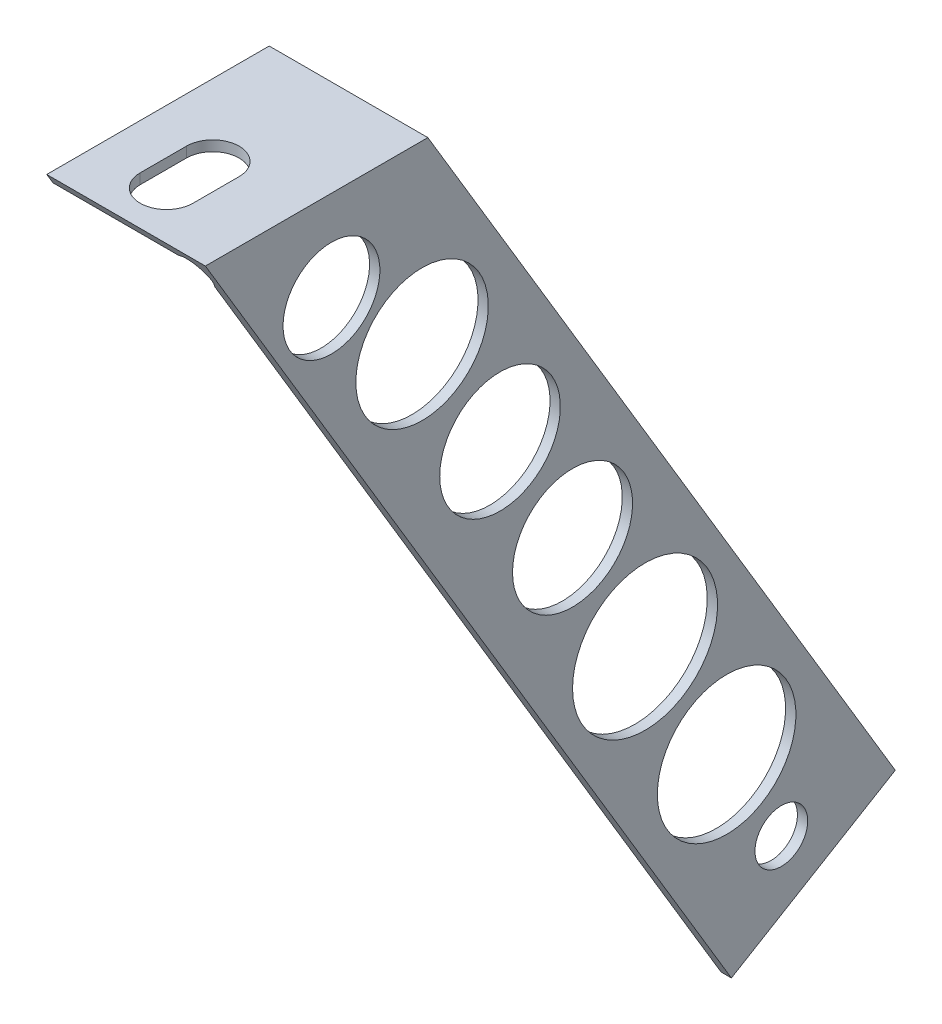
SolidWorks part; units mm, degrees
ref_plane "Front Plane" through (0, 0, 0) normal (0, 0, 1) x (1, 0, 0)
ref_plane "Top Plane" through (0, 0, 0) normal (0, 1, 0) x (1, 0, 0)
ref_plane "Right Plane" through (0, 0, 0) normal (1, 0, 0) x (0, 0, -1)
sketch "Sketch1" plane through (0, 0, 0) normal (1, 0, 0) x (0, 0, -1)
  line L0 (-193.675, 0) -> (193.675, 0)
  line L1 (193.675, 0) -> (239.395, -132.715)
  line L2 (239.395, -132.715) -> (239.395, -161.29)
  line L3 (239.395, -161.29) -> (-243.205, -161.29)
  line L4 (-243.205, -161.29) -> (-243.205, -132.715)
  line L5 (-243.205, -132.715) -> (-193.675, 0)
  line L6 (219.075, -116.84) -> (219.075, 0) construction
  line L7 (219.075, -116.84) -> (233.9261, -116.84) construction
  line L8 (142.875, 0) -> (142.875, -116.84) construction
  line L9 (219.075, -116.84) -> (219.075, -161.29) construction
  circle A0 centre (219.075, -116.84) radius 4.064
  circle A1 centre (219.075, -116.84) radius 8.6233 construction
  circle A2 centre (142.875, 0) radius 4.064 construction
  circle A3 centre (-31.115, 0) radius 4.064 construction
  point P9 (0, 0)
  dimension "D8" = 8.128
  dimension "D11" = 17.2466
  dimension "D3" = 8.128
  dimension "D9" = 8.128
  dimension "D1" = 387.35
  dimension "D2" = 173.99
  dimension "D4" = 482.6
  dimension "D5" = 110.466
  dimension "D6" = 20.32
  dimension "D7" = 161.29
  dimension "D10" = 116.84
  dimension "D12" = 76.2
  dimension "D13" = 50.8
extrude "Boss-Extrude1" add sketch "Sketch1" along normal blind 2.032
sketch "Sketch2" plane through (0, 0, 0) normal (0, 1, 0) x (1, 0, 0)
  line L2 (-13.843, 144.8435) -> (-13.843, 137.7315)
  line L4 (-5.715, 144.8435) -> (-5.715, 137.7315)
  line L5 (2.032, -193.675) -> (2.032, 193.675)
  line L6 (2.032, 193.675) -> (0, 193.675)
  line L7 (0, 193.675) -> (-20.828, 165.1)
  line L8 (-20.828, 165.1) -> (-20.828, -165.1)
  line L9 (-20.828, -165.1) -> (0, -193.675)
  line L10 (0, -193.675) -> (2.032, -193.675)
  line L11 (-13.843, 144.8435) -> (-5.715, 137.7315) construction
  line L12 (-13.843, 137.7315) -> (-5.715, 144.8435) construction
  circle A0 centre (-9.779, 141.2875) radius 4.064 construction
  circle A1 centre (-9.779, -32.7025) radius 4.064
  arc A2 (-13.843, 144.8435) -> (-5.715, 144.8435) centre (-9.779, 144.8435) cw
  arc A3 (-13.843, 137.7315) -> (-5.715, 137.7315) centre (-9.779, 137.7315) ccw
  point P0 (-20.828, 0)
  point P1 (2.032, 0)
  point P22 (-9.779, 148.9075)
  point P23 (-9.779, 133.6675)
  dimension "D3" = 8.128
  dimension "D4" = 8.128
  dimension "D5" = 15.24
  dimension "D9" = 173.99
  dimension "D1" = 22.86
  dimension "D2" = 330.2
  dimension "D6" = 11.811
  dimension "D8" = 11.811
  dimension "D11" = 52.3875
extrude "Boss-Extrude2" add sketch "Sketch2" along normal blind 2.032
fillet "Fillet1" radius 2.032 1 edges at (2.032, 2.032, 0)
sketch "Sketch3" plane through (0, 0, 0) normal (0, 0, 1) x (1, 0, 0)
  line L1 (0, 2.032) -> (-20.828, 2.032) construction
  line L4 (2.032, -132.715) -> (2.032, 0) construction
  line L7 (2.032, -161.29) -> (2.032, -132.715) construction
  line L9 (-1.376, 2.032) -> (-20.828, 2.032)
  line L12 (2.032, -132.715) -> (2.032, -1.376)
  line L15 (2.032, -161.29) -> (2.032, -132.715)
  line L16 (-20.828, 2.032) -> (-20.828, 3.6195)
  line L17 (-20.828, 3.6195) -> (3.6195, 3.6195)
  line L18 (3.6195, 3.6195) -> (3.6195, -161.29)
  line L19 (3.6195, -161.29) -> (2.032, -161.29)
  arc A2 (-1.376, 2.032) -> (2.032, -1.376) centre (0, 0) cw
  dimension "D1" = 1.5875
  dimension "D2" = 1.5875
extrude "Boss-Extrude3" add sketch "Sketch3" against normal up to surface (239.395 mm away) and the other way blind 58.42 up to face at (1.016, -147.0025, -239.395)
ref_point "Point1"
ref_point "Point2"
ref_point "Point3"
sketch "Sketch4" plane through (0, 0, -239.395) normal (0, 0, -1) x (-1, 0, 0)
  line L0 (0, -161.29) -> (44.2631, -161.29)
  line L1 (44.2631, -161.29) -> (44.2631, 7.3909)
  line L2 (44.2631, 7.3909) -> (27.6363, 7.3909)
  line L3 (-2.032, -132.715) -> (-2.032, -161.29)
  line L4 (-3.6195, -161.29) -> (0, -161.29) construction
  line L5 (-2.032, -161.29) -> (0, -161.29)
  line L6 (20.828, 3.6195) -> (-3.6195, 3.6195)
  line L7 (20.828, 2.032) -> (20.828, 3.6195)
  line L8 (0, -161.29) -> (0, -132.715)
  line L9 (27.6363, 7.3909) -> (27.6363, 2.032)
  line L10 (-3.6195, -161.29) -> (0, -161.29)
  line L11 (-3.6195, 3.6195) -> (-3.6195, -161.29)
  line L23 (0, -132.715) -> (-2.032, -132.715)
  line L25 (-2.032, -132.715) -> (-2.032, -1.376)
  line L26 (-2.032, -132.715) -> (-2.032, -1.376)
  line L27 (1.376, 2.032) -> (20.828, 2.032)
  line L28 (1.376, 2.032) -> (27.6363, 2.032)
  arc A1 (1.376, 2.032) -> (-2.032, -1.376) centre (0, 0) ccw
  arc A4 (1.376, 2.032) -> (-2.032, -1.376) centre (0, 0) ccw
  dimension "D1" = 0
extrude "Cut-Extrude1" cut sketch "Sketch4" against normal through all both and the other way through all
sketch "Sketch6" plane through (3.6195, 0, 0) normal (1, 0, 0) x (0, 0, -1)
  line L0 (164.5934, 3.6195) -> (236.6304, -116.84)
  line L1 (-58.42, 3.6195) -> (239.395, 3.6195) construction
  line L2 (236.6304, -116.84) -> (211.3757, -131.9428)
  line L3 (211.3757, -131.9428) -> (130.307, 3.6195)
  line L4 (130.307, 3.6195) -> (-58.42, 3.6195)
  line L5 (-58.42, 3.6195) -> (-58.42, -161.29)
  line L6 (-58.42, -161.29) -> (239.395, -161.29)
  line L7 (239.395, -161.29) -> (239.395, 3.6195)
  line L8 (239.395, 3.6195) -> (164.5934, 3.6195)
extrude "Cut-Extrude2" cut sketch "Sketch6" against normal through all
sketch "Sketch7" plane through (3.6195, 0, 0) normal (1, 0, 0) x (0, 0, -1)
  circle A0 centre (219.075, -116.84) radius 4.064
  point P3 (0, 0)
  dimension "D1" = 8.128
extrude "Cut-Extrude3" cut sketch "Sketch7" against normal through all
sketch "Sketch8" plane through (0, 3.6195, 0) normal (0, 1, 0) x (1, 0, 0)
  line L2 (-13.843, 144.8435) -> (-13.843, 137.7315)
  line L4 (-5.715, 144.8435) -> (-5.715, 137.7315)
  line L5 (-13.843, 144.8435) -> (-5.715, 137.7315) construction
  line L6 (-13.843, 137.7315) -> (-5.715, 144.8435) construction
  circle A1 centre (-9.779, -32.7025) radius 4.064
  arc A2 (-13.843, 144.8435) -> (-5.715, 144.8435) centre (-9.779, 144.8435) cw
  arc A3 (-5.715, 137.7315) -> (-13.843, 137.7315) centre (-9.779, 137.7315) cw
  point P0 (-9.779, 141.2875)
  point P11 (-9.779, 148.9075)
  point P12 (-9.779, 133.6675)
  dimension "D1" = 15.24
  dimension "D2" = 8.128
  dimension "D3" = 8.128
extrude "Cut-Extrude4" cut sketch "Sketch8" against normal through all
sketch "Sketch10" plane through (2.032, 0, 0) normal (-1, 0, 0) x (0, 0, 1)
  circle A0 centre (-210.6422, -101.738) radius 10.6768
  circle A1 centre (-186.895, -60.9488) radius 9.2512
  circle A2 centre (-175.7199, -42.5098) radius 9.2944
  circle A3 centre (-163.7066, -23.5121) radius 10.2077
  circle A4 centre (-149.7377, -10.3813) radius 7.4606
  circle A5 centre (-198.0701, -81.064) radius 11.174
  point P10 (-198.8818, -82.1815)
  point P11 (-210.6422, -101.738)
  point P12 (-149.7377, -10.3813)
  point P13 (-163.7066, -23.5121)
  point P16 (-175.7199, -42.5098)
  point P17 (-186.895, -60.9488)
  point P18 (-198.0701, -81.064)
extrude "Cut-Extrude5" cut sketch "Sketch10" against normal through all
